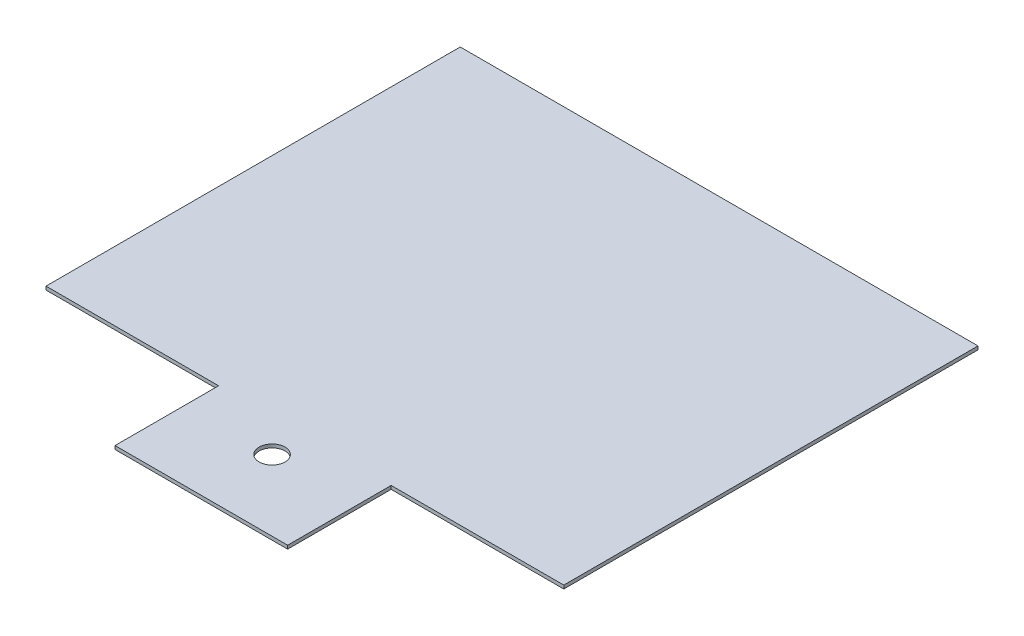
SolidWorks part; units mm, degrees
ref_plane "Front Plane" through (0, 0, 0) normal (0, 0, 1) x (1, 0, 0)
ref_plane "Top Plane" through (0, 0, 0) normal (0, 1, 0) x (1, 0, 0)
ref_plane "Right Plane" through (0, 0, 0) normal (1, 0, 0) x (0, 0, -1)
sketch "Sketch1" plane through (0, 0, 0) normal (0, 1, 0) x (1, 0, 0)
  line L0 (-50, 250) -> (-150, 250)
  line L1 (-50, -50) -> (50, -50)
  line L2 (-50, -50) -> (-50, 10)
  line L3 (-50, 250) -> (50, 250)
  line L4 (50, -50) -> (50, 10)
  line L5 (-50, -50) -> (0, 0) construction
  line L6 (0, 0) -> (50, -50) construction
  line L7 (-150, 250) -> (-150, 10)
  line L8 (-150, 10) -> (-50, 10)
  line L9 (50, 10) -> (150, 10)
  line L10 (150, 10) -> (150, 250)
  line L11 (150, 250) -> (50, 250)
  point P0 (0, 0)
  dimension "D1" = 300
  dimension "D2" = 100
  dimension "D3" = 100
  dimension "D4" = 240
  dimension "D5" = 100
extrude "Boss-Extrude1" add sketch "Sketch1" along normal blind 2
sketch "Sketch2" plane through (0, 0, 0) normal (0, -1, 0) x (-1, 0, 0)
  circle A0 centre (0, -9) radius 7.5
extrude "Cut-Extrude1" cut sketch "Sketch2" against normal blind 10
